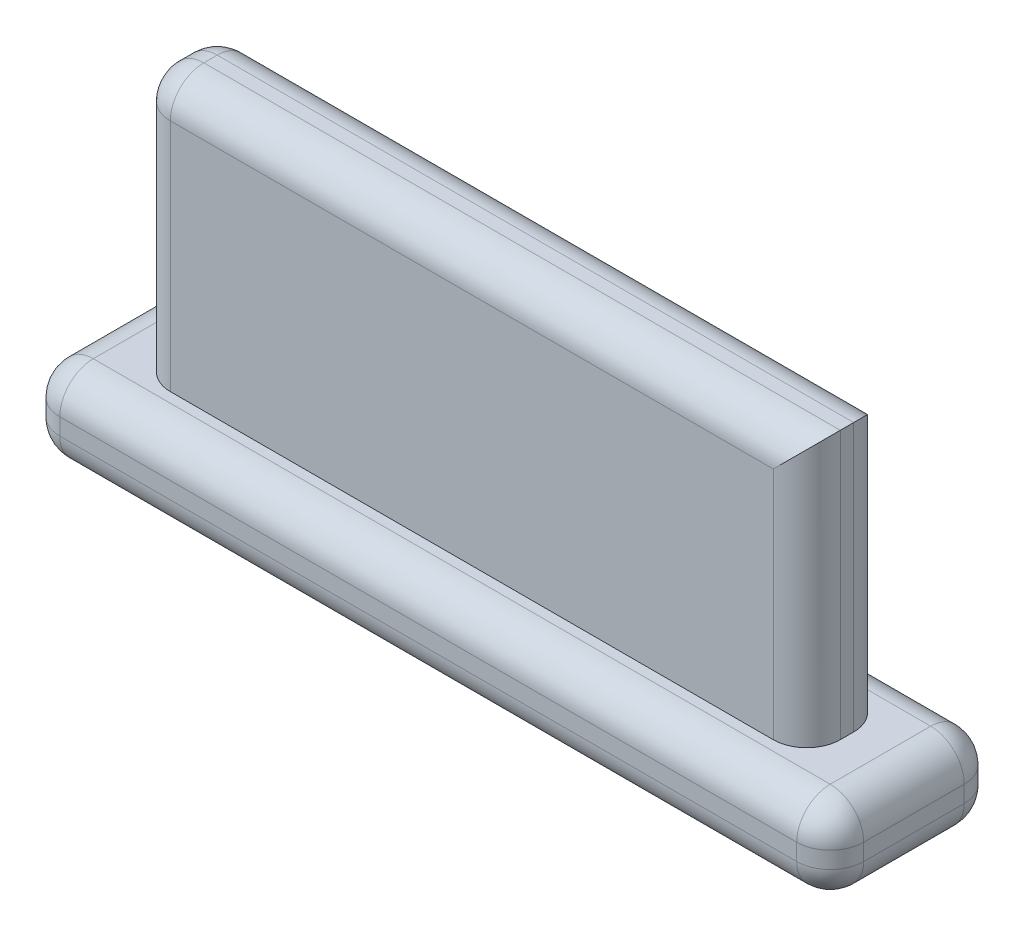
SolidWorks part; units mm, degrees
ref_plane "Front Plane" through (0, 0, 0) normal (0, 0, 1) x (1, 0, 0)
ref_plane "Top Plane" through (0, 0, 0) normal (0, 1, 0) x (1, 0, 0)
ref_plane "Right Plane" through (0, 0, 0) normal (1, 0, 0) x (0, 0, -1)
sketch "Sketch3" [suppressed] plane through (0, 0, 0) normal (0, 1, 0) x (1, 0, 0)
  line L1 (-38.1, 19.05) -> (38.1, 19.05)
  line L2 (-38.1, 19.05) -> (-38.1, -19.05)
  line L3 (-38.1, -19.05) -> (38.1, -19.05)
  line L4 (38.1, 19.05) -> (38.1, -19.05)
  line L5 (-38.1, 19.05) -> (38.1, -19.05) construction
  line L6 (-38.1, -19.05) -> (38.1, 19.05) construction
  point P0 (0, 0)
  dimension "D1" = 76.2
  dimension "D2" = 38.1
extrude "Boss-Extrude3" [suppressed] add sketch "Sketch3" along normal blind 1
sketch "Sketch1" plane through (0, 0, 0) normal (0, 1, 0) x (1, 0, 0)
  line L1 (-12.7, -1.524) -> (12.7, -1.524)
  line L2 (-12.7, -1.524) -> (-12.7, 1.524)
  line L3 (-12.7, 1.524) -> (12.7, 1.524)
  line L4 (12.7, -1.524) -> (12.7, 1.524)
  line L5 (-12.7, -1.524) -> (12.7, 1.524) construction
  line L6 (-12.7, 1.524) -> (12.7, -1.524) construction
  point P0 (0, 0)
  dimension "D1" = 25.4
  dimension "D2" = 3.048
extrude "Boss-Extrude1" add sketch "Sketch1" along normal blind 10.16
sketch "Sketch2" plane through (0, 0, 0) normal (0, -1, 0) x (1, 0, 0)
  line L1 (-15.24, 3.175) -> (15.24, 3.175)
  line L2 (-15.24, 3.175) -> (-15.24, -3.175)
  line L3 (-15.24, -3.175) -> (15.24, -3.175)
  line L4 (15.24, 3.175) -> (15.24, -3.175)
  line L5 (-15.24, 3.175) -> (15.24, -3.175) construction
  line L6 (-15.24, -3.175) -> (15.24, 3.175) construction
  point P0 (0, 0)
  dimension "D1" = 30.48
  dimension "D2" = 6.35
extrude "Boss-Extrude2" add sketch "Sketch2" along normal blind 3.175
fillet "Fillet1" radius 1.27 19 edges at (0, -3.175, 3.175) (0, 0, 3.175) (15.24, -3.175, 0) (15.24, -1.5875, 3.175) (15.24, 0, 0) (-15.24, -1.5875, 3.175) (-15.24, -3.175, 0) (-15.24, 0, 0) (-15.24, -1.5875, -3.175) (0, -3.175, -3.175) (15.24, -1.5875, -3.175) (0, 0, -3.175) (0, 10.16, 1.524) (-12.7, 5.08, -1.524) (-12.7, 5.08, 1.524) (12.7, 5.08, -1.524) (12.7, 5.08, 1.524) (0, 10.16, -1.524) (-12.7, 10.16, 0)
